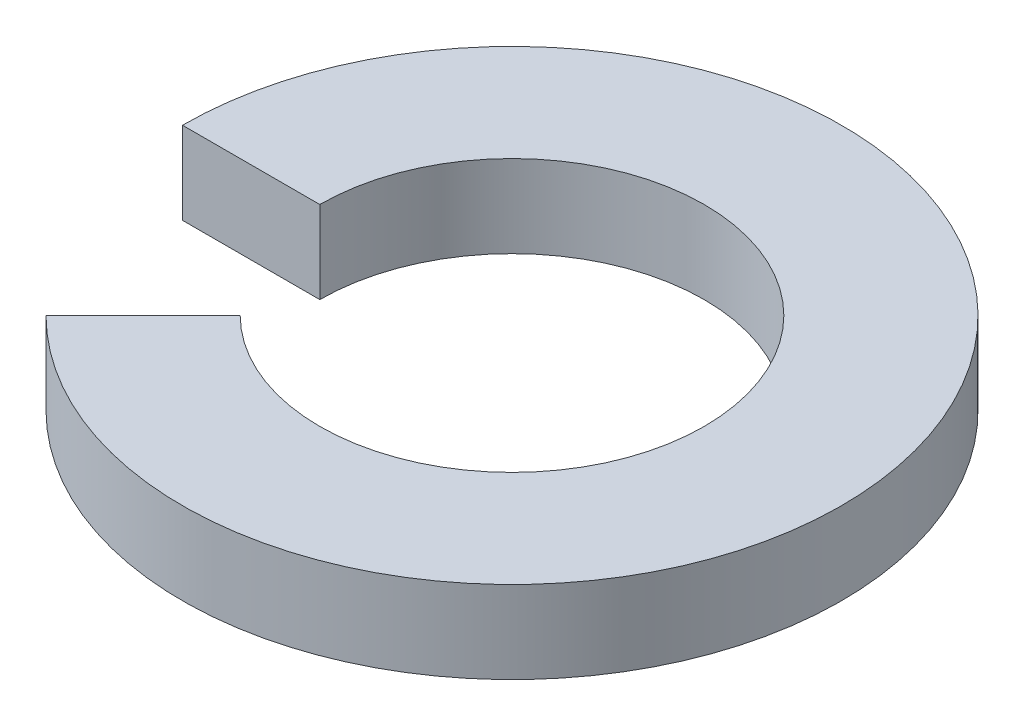
SolidWorks part; units mm, degrees
ref_plane "Front Plane" through (0, 0, 0) normal (0, 0, 1) x (1, 0, 0)
ref_plane "Top Plane" through (0, 0, 0) normal (0, 1, 0) x (1, 0, 0)
ref_plane "Right Plane" through (0, 0, 0) normal (1, 0, 0) x (0, 0, -1)
sketch "Sketch1" plane through (0, 0, 0) normal (0, 1, 0) x (1, 0, 0)
  line L0 (0, 0) -> (-6, 0)
  line L1 (0, 0) -> (-4.2426, -4.2426)
  arc A0 (-2.4749, -2.4749) -> (-3.5, 0) centre (0, 0) ccw
  arc A1 (-4.2426, -4.2426) -> (-6, 0) centre (0, 0) ccw
  dimension "D1" = 7
  dimension "D2" = 12
  dimension "D3" = 45
extrude "Boss-Extrude1" add sketch "Sketch1" along normal blind 1.5 contours L1 A1 L0 A0
